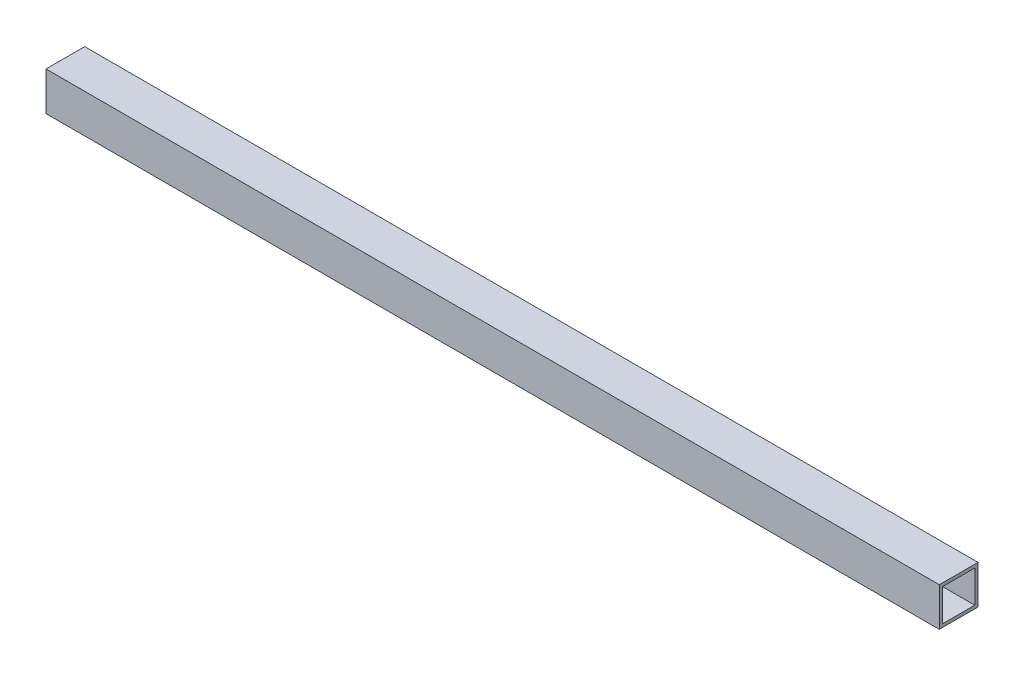
SolidWorks part; units mm, degrees
material "6061 Alloy"
ref_plane "Front Plane" through (0, 0, 0) normal (0, 0, 1) x (1, 0, 0)
ref_plane "Top Plane" through (0, 0, 0) normal (0, 1, 0) x (1, 0, 0)
ref_plane "Right Plane" through (0, 0, 0) normal (1, 0, 0) x (0, 0, -1)
sketch "Sketch1" plane through (0, 0, 0) normal (1, 0, 0) x (0, 0, -1)
  line L0 (9.525, 9.525) -> (-9.525, 9.525)
  line L1 (9.525, 9.525) -> (9.525, -9.525)
  line L2 (-9.525, 9.525) -> (-9.525, -9.525)
  line L3 (9.525, -9.525) -> (-9.525, -9.525)
  line L4 (9.525, 9.525) -> (-9.525, -9.525) construction
  line L5 (-9.525, 9.525) -> (9.525, -9.525) construction
  line L6 (7.9375, -7.9375) -> (7.9375, 7.9375)
  line L7 (7.9375, -7.9375) -> (-7.9375, -7.9375)
  line L8 (7.9375, 7.9375) -> (-7.9375, 7.9375)
  line L9 (-7.9375, -7.9375) -> (-7.9375, 7.9375)
  line L10 (7.9375, -7.9375) -> (-7.9375, 7.9375) construction
  line L11 (7.9375, 7.9375) -> (-7.9375, -7.9375) construction
  line L12 (7.9375, 9.525) -> (7.9375, 7.9375) construction
  line L13 (7.9375, 7.9375) -> (9.525, 7.9375) construction
  line L14 (-7.9375, -9.525) -> (-7.9375, -7.9375) construction
  line L15 (-7.9375, -7.9375) -> (-9.525, -7.9375) construction
  point P1 (0, 0)
  point P2 (0, 0)
  dimension "D1" = 19.05
  dimension "D2" = 1.5875
extrude "Boss-Extrude1" add sketch "Sketch1" along normal blind 440
